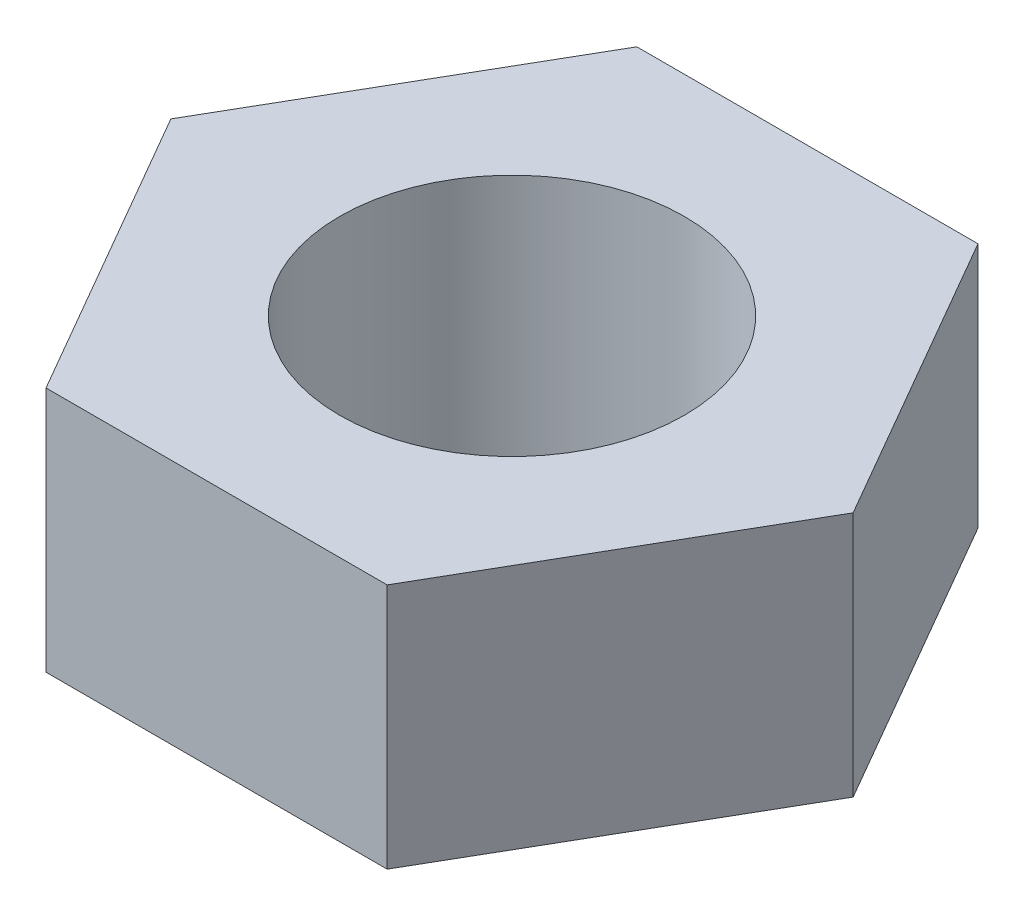
SolidWorks part; units mm, degrees
ref_plane "Front Plane" through (0, 0, 0) normal (0, 0, 1) x (1, 0, 0)
ref_plane "Top Plane" through (0, 0, 0) normal (0, 1, 0) x (1, 0, 0)
ref_plane "Right Plane" through (0, 0, 0) normal (1, 0, 0) x (0, 0, -1)
sketch "Sketch1" plane through (0, 0, 0) normal (0, 1, 0) x (1, 0, 0)
  line L1 (13.8564, 0) -> (6.9282, 12)
  line L2 (6.9282, 12) -> (-6.9282, 12)
  line L3 (-6.9282, 12) -> (-13.8564, 0)
  line L4 (-13.8564, 0) -> (-6.9282, -12)
  line L5 (-6.9282, -12) -> (6.9282, -12)
  line L6 (6.9282, -12) -> (13.8564, 0)
  circle A0 centre (0, 0) radius 12 construction
  circle A1 centre (0, 0) radius 7
  point P10 (0, 0)
  dimension "D1" = 14
  dimension "D2" = 24
extrude "Boss-Extrude1" add sketch "Sketch1" along normal blind 10
